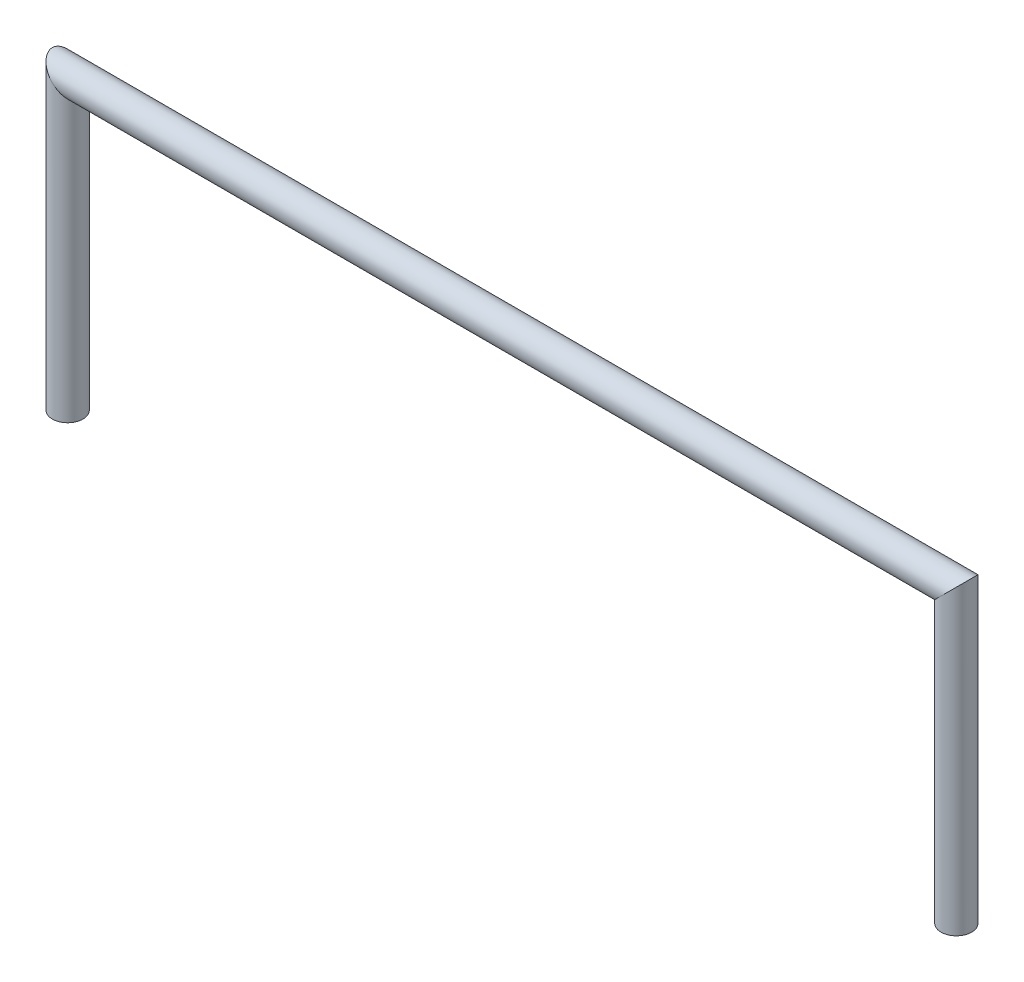
SolidWorks part; units mm, degrees
material "Cast Carbon Steel"
ref_plane "Front Plane" through (0, 0, 0) normal (0, 0, 1) x (1, 0, 0)
ref_plane "Top Plane" through (0, 0, 0) normal (0, 1, 0) x (1, 0, 0)
ref_plane "Right Plane" through (0, 0, 0) normal (1, 0, 0) x (0, 0, -1)
sketch "Sketch1" plane through (0, 0, 0) normal (0, 0, 1) x (1, 0, 0)
  line L0 (0, 0) -> (0, 241.3)
  line L1 (0, 241.3) -> (736.6, 241.3)
  line L2 (736.6, 241.3) -> (736.6, 0)
  dimension "D1" = 241.3
  dimension "D2" = 736.6
sketch "Sketch3" plane through (0, 0, 0) normal (0, 1, 0) x (1, 0, 0)
  circle A0 centre (0, 0) radius 12.7
  circle A1 centre (0, 0) radius 8.7312
  dimension "D1" = 25.4
  dimension "D2" = 17.4625
sweep "Sweep1" add profiles "Sketch3" path "Sketch1"
